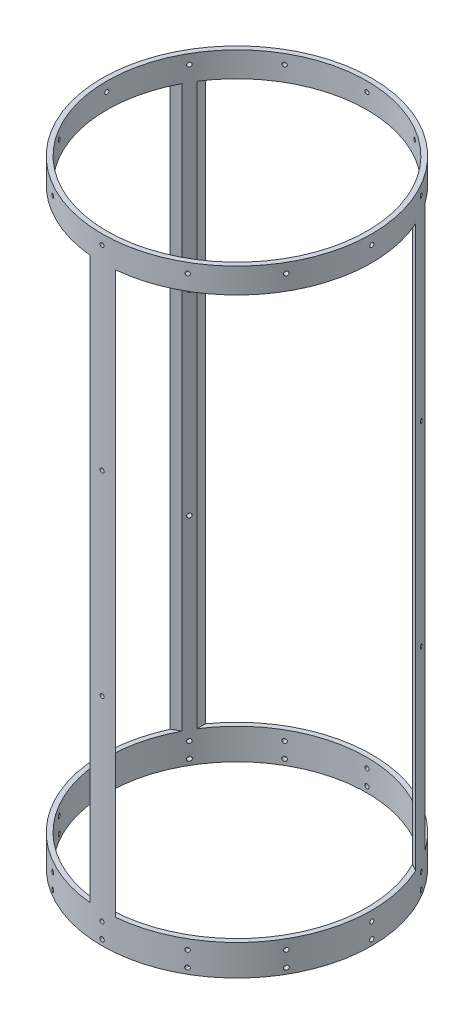
SolidWorks part; units mm, degrees
material "6061-T6 (SS)"
ref_plane "Front Plane" through (0, 0, 0) normal (0, 0, 1) x (1, 0, 0)
ref_plane "Top Plane" through (0, 0, 0) normal (0, 1, 0) x (1, 0, 0)
ref_plane "Right Plane" through (0, 0, 0) normal (1, 0, 0) x (0, 0, -1)
sketch "Sketch1" plane through (0, 0, 0) normal (0, 1, 0) x (1, 0, 0)
  circle A0 centre (0, 0) radius 88.9
  circle A1 centre (0, 0) radius 85.725
  dimension "D1" = 177.8
  dimension "D2" = 171.45
extrude "Boss-Extrude1" add sketch "Sketch1" along normal mid plane 406.4
sketch "Sketch2" plane through (0, 0, 0) normal (0, 0, 1) x (1, 0, 0)
  line L0 (85.725, 203.2) -> (-85.725, 203.2) construction
  line L1 (-72.39, -182.88) -> (72.39, -182.88)
  line L2 (-72.39, -182.88) -> (-72.39, 186.69)
  line L3 (-72.39, 186.69) -> (72.39, 186.69)
  line L4 (72.39, -182.88) -> (72.39, 186.69)
  line L5 (-72.39, -182.88) -> (72.39, 186.69) construction
  line L6 (-72.39, 186.69) -> (72.39, -182.88) construction
  line L7 (88.9, -203.2) -> (88.9, 203.2) construction
  line L8 (-88.9, 203.2) -> (-88.9, -203.2) construction
  line L9 (-88.9, -203.2) -> (88.9, -203.2) construction
  point P0 (0, 0)
  dimension "D1" = 16.51
  dimension "D2" = 16.51
  dimension "D3" = 16.51
  dimension "D4" = 20.32
extrude "Cut-Extrude1" cut sketch "Sketch2" against normal up to surface (51.6033 mm away)
pattern_circular "CirPattern1" count 3 over 360 about axis through (0, 0, 0) along (0, 1, 0) of "Cut-Extrude1"
ref_plane "Plane1" through (88.9, 0, 0) normal (1, 0, 0) x (0, 0, -1)
sketch "Sketch3" plane through (88.9, 0, 0) normal (1, 0, 0) x (0, 0, -1)
  line L0 (36.8899, -182.88) -> (-88.4932, -182.88) construction
  line L1 (-88.9, -203.2) -> (88.9, -203.2) construction
  circle A0 centre (0, -199.39) radius 1.4351
  circle A1 centre (0, -189.23) radius 1.3525
  dimension "D1" = 3.81
  dimension "D2" = 2.8702
  dimension "D3" = 2.7051
  dimension "D4" = 6.35
extrude "Cut-Extrude2" cut sketch "Sketch3" against normal blind 15.24
pattern_circular "CirPattern2" count 12 over 360 about axis through (0, 203.2, 0) along (0, -1, 0) of "Cut-Extrude2"
sketch "Sketch4" plane through (88.9, 0, 0) normal (1, 0, 0) x (0, 0, -1)
  line L0 (0, 97.79) -> (0, -97.79) construction
  line L1 (88.9, 203.2) -> (-88.9, 203.2) construction
  circle A0 centre (0, 196.85) radius 1.3525
  dimension "D1" = 2.7051
  dimension "D2" = 6.35
extrude "Cut-Extrude3" cut sketch "Sketch4" against normal blind 15.24
pattern_circular "CirPattern3" count 12 over 360 about axis through (0, 203.2, 0) along (0, -1, 0) of "Cut-Extrude3"
ref_plane "Plane2" through (0, 0, 88.9) normal (0, 0, 1) x (1, 0, 0)
sketch "Sketch5" plane through (0, 0, 88.9) normal (0, 0, 1) x (1, 0, 0)
  circle A0 centre (0, 68.1736) radius 1.3526
  circle A1 centre (0, -60.5536) radius 1.3526
  circle A2 centre (0, 196.85) radius 1.3525 construction
  circle A3 centre (0, -189.23) radius 1.3526 construction
  dimension "D1" = 128.6764
  dimension "D2" = 128.6764
  dimension "D3" = 2.7051
  dimension "D4" = 2.7051
extrude "Cut-Extrude4" cut sketch "Sketch5" against normal blind 35.56
pattern_circular "CirPattern4" count 3 over 360 about axis through (0, 203.2, 0) along (0, -1, 0) of "Cut-Extrude4"
